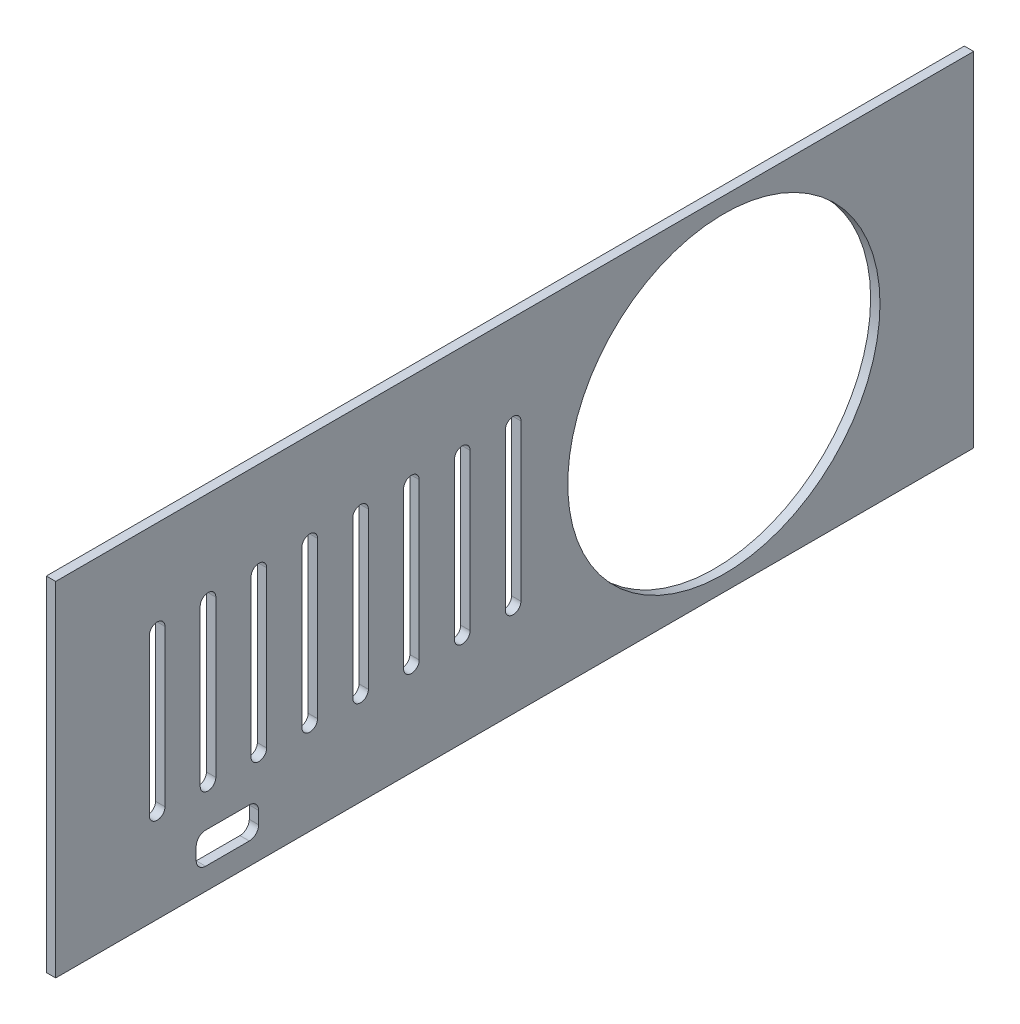
SolidWorks part; units mm, degrees
ref_plane "Ön Düzlem" through (0, 0, 0) normal (0, 0, 1) x (1, 0, 0)
ref_plane "Üst Düzlem" through (0, 0, 0) normal (0, 1, 0) x (1, 0, 0)
ref_plane "Sağ Düzlem" through (0, 0, 0) normal (1, 0, 0) x (0, 0, -1)
sketch "Çizim1" plane through (0, 0, 0) normal (1, 0, 0) x (0, 0, -1)
  line L1 (0, 0) -> (294, 0)
  line L2 (0, 0) -> (0, -110)
  line L3 (0, -110) -> (294, -110)
  line L4 (294, 0) -> (294, -110)
  dimension "D1" = 294
  dimension "D2" = 110
extrude "Yükseklik-Ekstrüzyon1" add sketch "Çizim1" along normal blind 3
sketch "Çizim2" plane through (3, 0, 0) normal (1, 0, 0) x (0, 0, -1)
  line L0 (294, -110) -> (294, 0) construction
  line L1 (32.5, -30) -> (32.5, -80) construction
  line L2 (35, -30) -> (35, -80)
  line L3 (30, -30) -> (30, -80)
  line L4 (0, 0) -> (0, -110) construction
  line L5 (46.2857, -30) -> (46.2857, -80)
  line L6 (51.2857, -30) -> (51.2857, -80)
  line L7 (48.7857, -30) -> (48.7857, -80) construction
  line L8 (62.5714, -30) -> (62.5714, -80)
  line L9 (67.5714, -30) -> (67.5714, -80)
  line L10 (65.0714, -30) -> (65.0714, -80) construction
  line L11 (78.8571, -30) -> (78.8571, -80)
  line L12 (83.8571, -30) -> (83.8571, -80)
  line L13 (81.3571, -30) -> (81.3571, -80) construction
  line L14 (95.1429, -30) -> (95.1429, -80)
  line L15 (100.1429, -30) -> (100.1429, -80)
  line L16 (97.6429, -30) -> (97.6429, -80) construction
  line L17 (111.4286, -30) -> (111.4286, -80)
  line L18 (116.4286, -30) -> (116.4286, -80)
  line L19 (113.9286, -30) -> (113.9286, -80) construction
  line L20 (127.7143, -30) -> (127.7143, -80)
  line L21 (132.7143, -30) -> (132.7143, -80)
  line L22 (130.2143, -30) -> (130.2143, -80) construction
  line L23 (144, -30) -> (144, -80)
  line L24 (149, -30) -> (149, -80)
  line L25 (146.5, -30) -> (146.5, -80) construction
  line L26 (0, -110) -> (294, -110) construction
  line L27 (48, -93) -> (62, -93)
  line L28 (45, -96) -> (45, -100)
  line L29 (48, -103) -> (62, -103)
  line L30 (65, -96) -> (65, -100)
  circle A0 centre (214, -55) radius 50
  arc A1 (35, -30) -> (30, -30) centre (32.5, -30) ccw
  arc A2 (30, -80) -> (35, -80) centre (32.5, -80) ccw
  arc A3 (51.2857, -30) -> (46.2857, -30) centre (48.7857, -30) ccw
  arc A4 (46.2857, -80) -> (51.2857, -80) centre (48.7857, -80) ccw
  arc A5 (67.5714, -30) -> (62.5714, -30) centre (65.0714, -30) ccw
  arc A6 (62.5714, -80) -> (67.5714, -80) centre (65.0714, -80) ccw
  arc A7 (83.8571, -30) -> (78.8571, -30) centre (81.3571, -30) ccw
  arc A8 (78.8571, -80) -> (83.8571, -80) centre (81.3571, -80) ccw
  arc A9 (100.1429, -30) -> (95.1429, -30) centre (97.6429, -30) ccw
  arc A10 (95.1429, -80) -> (100.1429, -80) centre (97.6429, -80) ccw
  arc A11 (116.4286, -30) -> (111.4286, -30) centre (113.9286, -30) ccw
  arc A12 (111.4286, -80) -> (116.4286, -80) centre (113.9286, -80) ccw
  arc A13 (132.7143, -30) -> (127.7143, -30) centre (130.2143, -30) ccw
  arc A14 (127.7143, -80) -> (132.7143, -80) centre (130.2143, -80) ccw
  arc A15 (149, -30) -> (144, -30) centre (146.5, -30) ccw
  arc A16 (144, -80) -> (149, -80) centre (146.5, -80) ccw
  arc A17 (45, -100) -> (48, -103) centre (48, -100) ccw
  arc A18 (62, -103) -> (65, -100) centre (62, -100) ccw
  arc A19 (62, -93) -> (65, -96) centre (62, -96) cw
  arc A20 (48, -93) -> (45, -96) centre (48, -96) ccw
  point P2 (32.5, -55)
  point P5 (294, -55)
  point P16 (48.7857, -55)
  point P23 (65.0714, -55)
  point P30 (81.3571, -55)
  point P37 (97.6429, -55)
  point P44 (113.9286, -55)
  point P51 (130.2143, -55)
  point P58 (146.5, -55)
  point P73 (65, -103)
  point P76 (65, -93)
  point P79 (32.5, -30.1854)
  point P80 (32.5, -48.4856)
  point P81 (32.5, -37.8102)
  point P82 (0, -55)
  dimension "D1" = 100
  dimension "D2" = 80
  dimension "D11" = 3
  dimension "D12" = 65
  dimension "D3" = 5
  dimension "D4" = 50
  dimension "D5" = 30
  dimension "D7" = 45
  dimension "D8" = 20
  dimension "D9" = 10
  dimension "D10" = 7
  dimension "D6" = 8
extrude "Kes-Ekstrüzyon1" cut sketch "Çizim2" against normal blind 3
